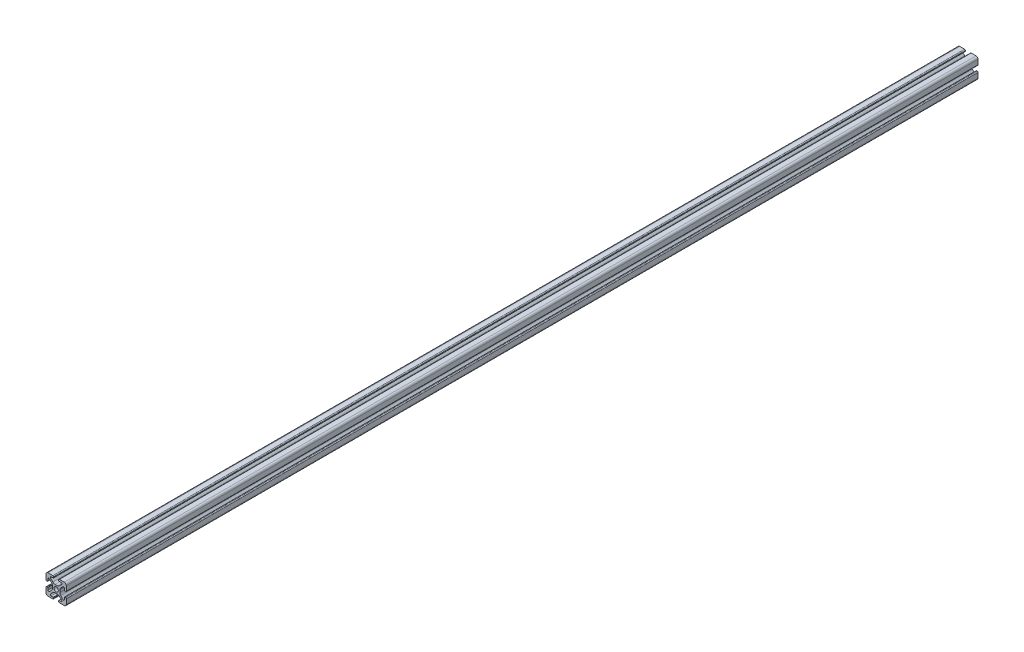
SolidWorks part; units mm, degrees
ref_plane "Front Plane" through (0, 0, 0) normal (0, 0, 1) x (1, 0, 0)
ref_plane "Top Plane" through (0, 0, 0) normal (0, 1, 0) x (1, 0, 0)
ref_plane "Right Plane" through (0, 0, 0) normal (1, 0, 0) x (0, 0, -1)
sketch "Sketch1" plane through (0, 0, 0) normal (0, 0, 1) x (1, 0, 0)
  line L0 (0, 10) -> (0, -10) construction
  line L1 (10, 0) -> (-10, 0) construction
  line L2 (-2.5, 10) -> (2.5, 10) construction
  line L3 (-5.75, 8.2) -> (5.75, 8.2) construction
  circle A0 centre (0, 0) radius 2.15 construction
  point P4 (0, 0)
  point P8 (0, 0)
  point P10 (0, 3.6)
  point P14 (0, 10)
  point P17 (0, 8.2)
  dimension "Thru Hole" = 4.3
  dimension "Height" = 20
  dimension "T Slot Depth" = 6.4
  dimension "T Slot Top Width" = 5
  dimension "T Slot Max Width" = 11.5
  dimension "Wall" = 1.8
sketch "Sketch2" plane through (0, 0, 0) normal (1, 0, 0) x (0, 0, -1)
  line L0 (450, 0) -> (-450, 0) construction
  point P4 (0, 0)
  dimension "D1" = 900
sketch "Sketch3" plane through (0, 0, 0) normal (0, 0, 1) x (1, 0, 0)
  line L0 (3.2874, 10) -> (8, 10)
  line L1 (10, 8) -> (10, -8) construction
  line L2 (8, -10) -> (-8, -10) construction
  line L3 (-10, 10) -> (10, -10) construction
  line L4 (2.5, 9.2126) -> (2.5, 8.5048)
  line L5 (-5.75, 8.2) -> (5.75, 8.2) construction
  line L6 (2.8048, 8.2) -> (4.9118, 8.2)
  line L7 (5.5045, 6.7691) -> (3.2141, 4.4787)
  line L8 (1.0928, 3.6) -> (-1.0928, 3.6)
  line L9 (0, 10) -> (0, -10) construction
  line L10 (5.75, 8.2) -> (5.75, 0) construction
  line L11 (10, 0) -> (-10, 0) construction
  line L12 (0, 0) -> (0, 10) construction
  line L13 (-2.5, 9.2126) -> (-2.5, 8.5048)
  line L14 (-5.5045, 6.7691) -> (-3.2141, 4.4787)
  line L15 (-2.8048, 8.2) -> (-4.9118, 8.2)
  line L16 (-3.2874, 10) -> (-8, 10)
  line L17 (0, 0) -> (-10, 0) construction
  line L18 (-10, 3.2874) -> (-10, 8)
  line L19 (-8.2, 2.8048) -> (-8.2, 4.9118)
  line L20 (-6.7691, 5.5045) -> (-4.4787, 3.2141)
  line L21 (-9.2126, 2.5) -> (-8.5048, 2.5)
  line L22 (-3.6, -1.0928) -> (-3.6, 1.0928)
  line L23 (-6.7691, -5.5045) -> (-4.4787, -3.2141)
  line L24 (-8.2, -2.8048) -> (-8.2, -4.9118)
  line L25 (-9.2126, -2.5) -> (-8.5048, -2.5)
  line L26 (-10, -3.2874) -> (-10, -8)
  line L27 (9.2126, -2.5) -> (8.5048, -2.5)
  line L28 (8.2, -2.8048) -> (8.2, -4.9118)
  line L29 (6.7691, -5.5045) -> (4.4787, -3.2141)
  line L30 (3.6, -1.0928) -> (3.6, 1.0928)
  line L31 (9.2126, 2.5) -> (8.5048, 2.5)
  line L32 (6.7691, 5.5045) -> (4.4787, 3.2141)
  line L33 (8.2, 2.8048) -> (8.2, 4.9118)
  line L34 (10, 8) -> (10, 3.2874)
  line L35 (10, -3.2874) -> (10, -8)
  line L36 (3.2874, -10) -> (8, -10)
  line L37 (-3.2874, -10) -> (-8, -10)
  line L38 (-6.7691, -5.5045) -> (-4.4787, -3.2141)
  line L39 (-2.8048, -8.2) -> (-4.9118, -8.2)
  line L40 (-5.5045, -6.7691) -> (-3.2141, -4.4787)
  line L41 (-2.5, -9.2126) -> (-2.5, -8.5048)
  line L42 (1.0928, -3.6) -> (-1.0928, -3.6)
  line L43 (5.5045, -6.7691) -> (3.2141, -4.4787)
  line L44 (2.8048, -8.2) -> (4.9118, -8.2)
  line L45 (2.5, -9.2126) -> (2.5, -8.5048)
  arc A0 (4.9118, 8.2) -> (5.5045, 6.7691) centre (4.9118, 7.3618) cw
  arc A1 (3.2141, 4.4787) -> (1.0928, 3.6) centre (1.0928, 6.6) cw
  circle A2 centre (0, 0) radius 2.15 construction
  circle A3 centre (0, 0) radius 2.15
  arc A4 (3.2874, 10) -> (2.5, 9.2126) centre (3.2874, 9.2126) ccw
  arc A5 (2.5, 8.5048) -> (2.8048, 8.2) centre (2.8048, 8.5048) ccw
  arc A6 (-3.2874, 10) -> (-2.5, 9.2126) centre (-3.2874, 9.2126) cw
  arc A7 (-4.9118, 8.2) -> (-5.5045, 6.7691) centre (-4.9118, 7.3618) ccw
  arc A8 (-3.2141, 4.4787) -> (-1.0928, 3.6) centre (-1.0928, 6.6) ccw
  arc A9 (-2.5, 8.5048) -> (-2.8048, 8.2) centre (-2.8048, 8.5048) cw
  arc A10 (-8.5048, 2.5) -> (-8.2, 2.8048) centre (-8.5048, 2.8048) ccw
  arc A11 (-4.4787, 3.2141) -> (-3.6, 1.0928) centre (-6.6, 1.0928) cw
  arc A12 (-8.2, 4.9118) -> (-6.7691, 5.5045) centre (-7.3618, 4.9118) cw
  arc A13 (-10, 3.2874) -> (-9.2126, 2.5) centre (-9.2126, 3.2874) ccw
  arc A14 (-8.5048, -2.5) -> (-8.2, -2.8048) centre (-8.5048, -2.8048) cw
  arc A15 (-10, -3.2874) -> (-9.2126, -2.5) centre (-9.2126, -3.2874) cw
  arc A16 (-4.4787, -3.2141) -> (-3.6, -1.0928) centre (-6.6, -1.0928) ccw
  arc A17 (-8.2, -4.9118) -> (-6.7691, -5.5045) centre (-7.3618, -4.9118) ccw
  arc A26 (-8, -10) -> (-10, -8) centre (-8, -8) cw
  arc A27 (-8, 10) -> (-10, 8) centre (-8, 8) ccw
  arc A28 (8, 10) -> (10, 8) centre (8, 8) cw
  arc A29 (10, -8) -> (8, -10) centre (8, -8) cw
  arc A30 (8.2, -4.9118) -> (6.7691, -5.5045) centre (7.3618, -4.9118) cw
  arc A31 (4.4787, -3.2141) -> (3.6, -1.0928) centre (6.6, -1.0928) cw
  arc A32 (10, -3.2874) -> (9.2126, -2.5) centre (9.2126, -3.2874) ccw
  arc A33 (8.5048, -2.5) -> (8.2, -2.8048) centre (8.5048, -2.8048) ccw
  arc A34 (10, 3.2874) -> (9.2126, 2.5) centre (9.2126, 3.2874) cw
  arc A35 (8.2, 4.9118) -> (6.7691, 5.5045) centre (7.3618, 4.9118) ccw
  arc A36 (4.4787, 3.2141) -> (3.6, 1.0928) centre (6.6, 1.0928) ccw
  arc A37 (8.5048, 2.5) -> (8.2, 2.8048) centre (8.5048, 2.8048) cw
  arc A38 (-2.5, -8.5048) -> (-2.8048, -8.2) centre (-2.8048, -8.5048) ccw
  arc A39 (-3.2141, -4.4787) -> (-1.0928, -3.6) centre (-1.0928, -6.6) cw
  arc A40 (-4.9118, -8.2) -> (-5.5045, -6.7691) centre (-4.9118, -7.3618) cw
  arc A41 (-3.2874, -10) -> (-2.5, -9.2126) centre (-3.2874, -9.2126) ccw
  arc A42 (2.5, -8.5048) -> (2.8048, -8.2) centre (2.8048, -8.5048) cw
  arc A43 (3.2874, -10) -> (2.5, -9.2126) centre (3.2874, -9.2126) cw
  arc A44 (3.2141, -4.4787) -> (1.0928, -3.6) centre (1.0928, -6.6) ccw
  arc A45 (4.9118, -8.2) -> (5.5045, -6.7691) centre (4.9118, -7.3618) ccw
  point P36 (2.5, 10)
  point P39 (2.5, 8.2)
  point P49 (0, 3.6)
  point P77 (-3.6, 0)
  point P78 (-8.2, -2.5)
  point P79 (-10, -2.5)
  point P104 (-10, -10)
  point P110 (10, 10)
  point P114 (10, -2.5)
  point P115 (8.2, -2.5)
  point P116 (3.6, 0)
  point P141 (0, -3.6)
  dimension "D1" = 3
  dimension "D2" = 0.8382
  dimension "D4" = 0.7874
  dimension "D5" = 0.3048
  dimension "D6" = 2
  dimension "D3" = 45
extrude "Boss-Extrude1" add sketch "Sketch3" along normal up to vertex (450 mm away) and the other way up to vertex (450 mm away) contours A45 L44 A42 L45 A43 L36 A29 L35 A32 L27 A33 L28 A30 L29 A31 L30 A36 L32 A35 L33 A37 L31 A34 L34 A28 L0 A4 L4 A5 L6 A0 L7 A1 L8 A8 L14 A7 L15 A9 L13 A6 L16 A27 L18 A13 L21 A10 L19 A12 L20 A11 up to point (0, 0, 450) other way up to point (0, 0, -450)
